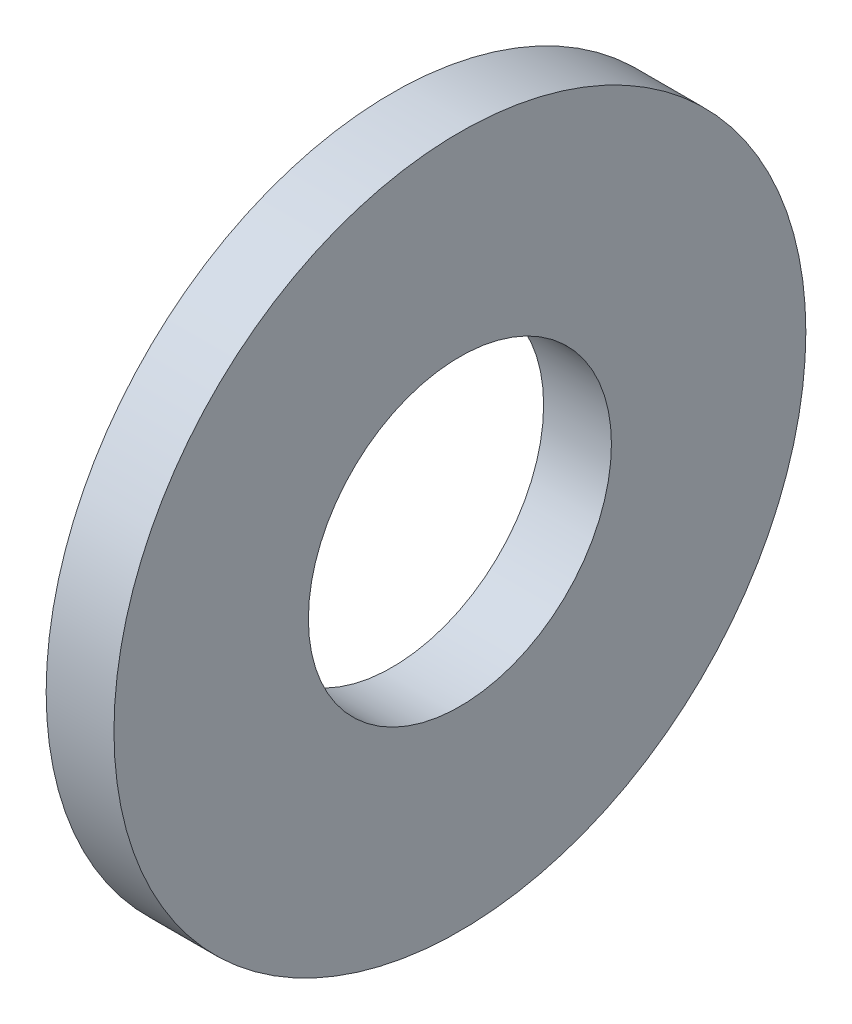
SolidWorks part; units mm, degrees
ref_plane "Plane1" through (0, 0, 0) normal (0, 0, 1) x (1, 0, 0)
ref_plane "Plane2" through (0, 0, 0) normal (0, 1, 0) x (1, 0, 0)
ref_plane "Plane3" through (0, 0, 0) normal (1, 0, 0) x (0, 0, -1)
sketch "Sketch1" plane through (0, 0, 0) normal (0, 0, 1) x (1, 0, 0)
  line L0 (-34.925, 0) -> (9.525, 0) construction
  line L1 (0, 2.7813) -> (0, 6.35)
  line L2 (0, 6.35) -> (-1.2446, 6.35)
  line L3 (-1.2446, 6.35) -> (-1.2446, 2.7813)
  line L4 (-1.2446, 2.7813) -> (0, 2.7813)
  dimension "Thickness" = 1.2446
  dimension "Inside_dia" = 5.5626
  dimension "Outside_dia" = 12.7
revolve "Base-Revolve" add sketch "Sketch1" angle 360 about L0
